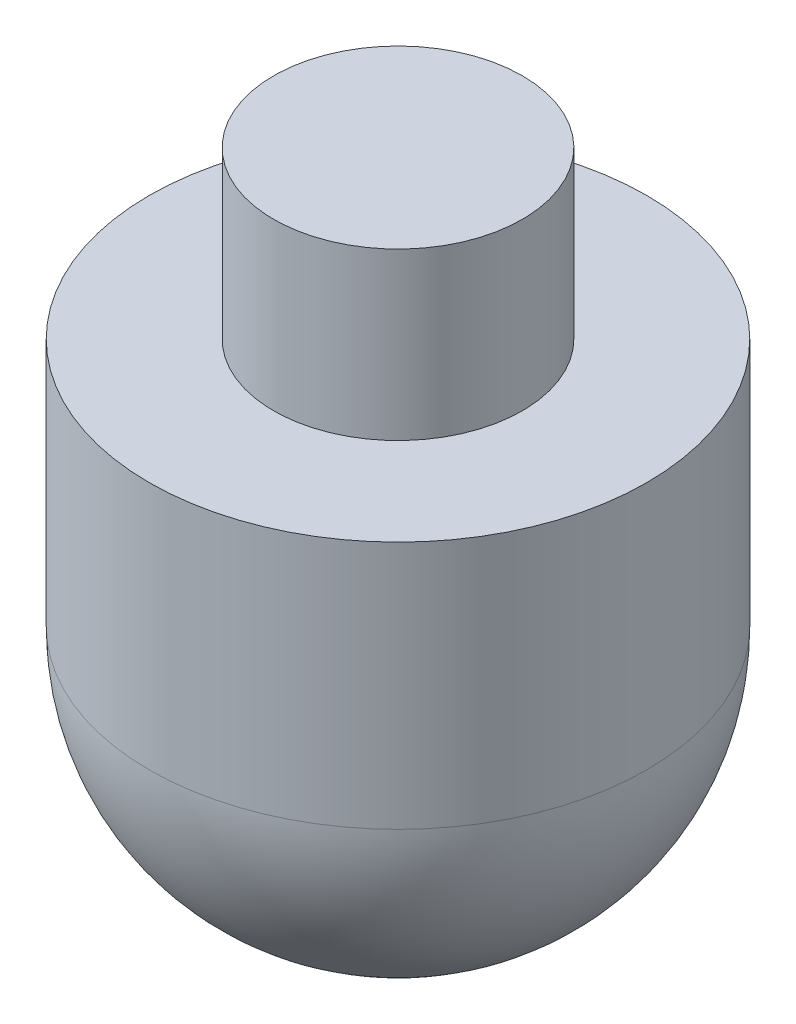
SolidWorks part; units mm, degrees
ref_plane "Front Plane" through (0, 0, 0) normal (0, 0, 1) x (1, 0, 0)
ref_plane "Top Plane" through (0, 0, 0) normal (0, 1, 0) x (1, 0, 0)
ref_plane "Right Plane" through (0, 0, 0) normal (1, 0, 0) x (0, 0, -1)
sketch "Sketch1" plane through (0, 0, 0) normal (0, 0, 1) x (1, 0, 0)
  line L0 (0, 1.7049) -> (0, 58.3869) construction
  line L1 (0, 41.7049) -> (7.5, 41.7049)
  line L2 (7.5, 41.7049) -> (7.5, 31.7049)
  line L3 (7.5, 31.7049) -> (15, 31.7049)
  line L4 (15, 31.7049) -> (15, 1.7049)
  line L5 (15, 1.7049) -> (0, 1.7049)
  line L6 (0, 1.7049) -> (0, 41.7049)
  dimension "D1" = 15
  dimension "D2" = 30
  dimension "D3" = 40
  dimension "D4" = 10
revolve "Revolve1" add sketch "Sketch1" angle 360 about L0
fillet "Fillet1" radius 15 1 edges at (0, 1.7049, -15)
